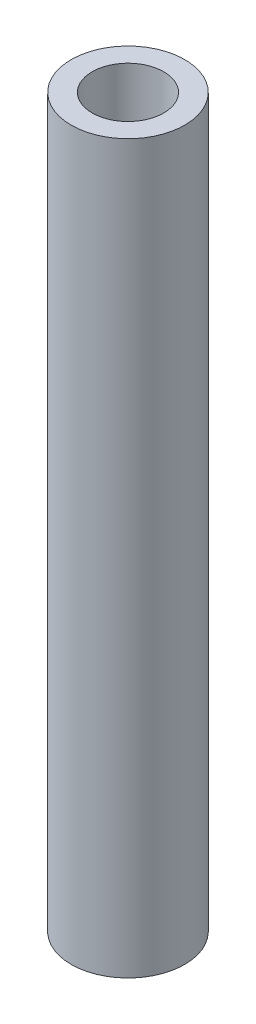
SolidWorks part; units mm, degrees
material "6061-T6 (SS)"
ref_plane "X-Y Datum" through (0, 0, 0) normal (0, 0, 1) x (1, 0, 0)
ref_plane "X-Z Datum" through (0, 0, 0) normal (0, 1, 0) x (1, 0, 0)
ref_plane "Y-Z Datum" through (0, 0, 0) normal (1, 0, 0) x (0, 0, -1)
sketch "Sketch1" plane through (0, 0, 0) normal (0, 1, 0) x (1, 0, 0)
  circle A0 centre (0, 0) radius 3.175
  circle A1 centre (0, 0) radius 2
  dimension "D1" = 6.35
  dimension "D2" = 4
extrude "Boss-Extrude1" add sketch "Sketch1" against normal blind 40.64
